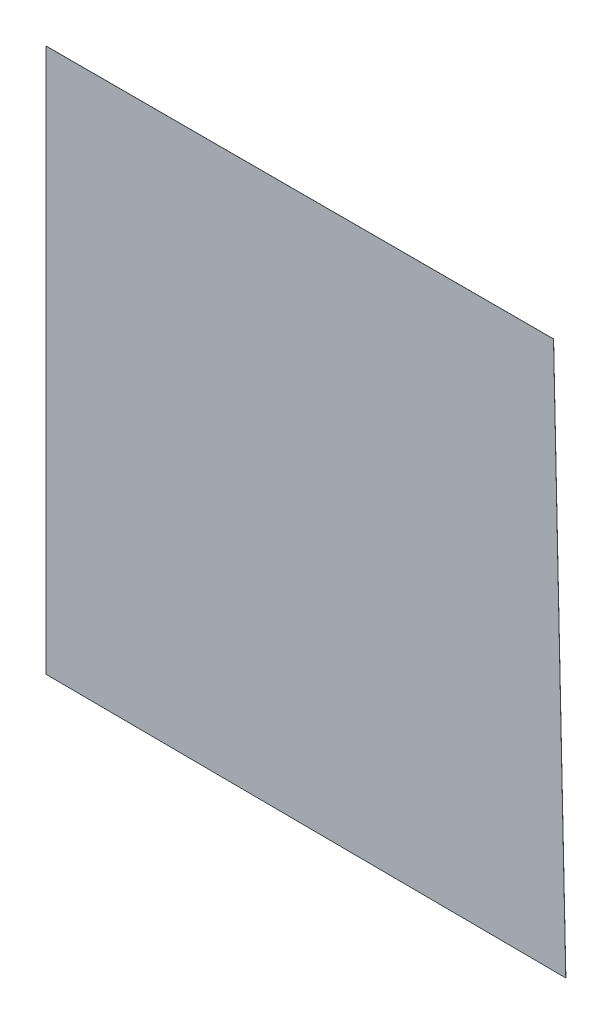
SolidWorks part; units mm, degrees
ref_plane "Alzado" through (0, 0, 0) normal (0, 0, 1) x (1, 0, 0)
ref_plane "Planta" through (0, 0, 0) normal (0, 1, 0) x (1, 0, 0)
ref_plane "Vista lateral" through (0, 0, 0) normal (1, 0, 0) x (0, 0, -1)
sketch "Croquis1" plane through (0, 0, 0) normal (0, 0, 1) x (1, 0, 0)
  line L0 (0, 0) -> (367.8609, -3505.2)
  line L1 (367.8609, -3505.2) -> (-11732.6991, -3406.3005)
  line L2 (-11732.6991, -3406.3005) -> (-11732.6991, 1226.6595)
  line L3 (-11732.6991, 1226.6595) -> (-6764.6695, 1180.9395)
  line L4 (-6764.6695, 1180.9395) -> (-6581.5791, -3448.4013)
  line L5 (-11732.6991, 1226.6595) -> (-11732.6991, 5798.6595)
  line L7 (-6764.6695, 1180.9395) -> (-6764.6695, 5844.3795)
  line L8 (-6764.6695, 1180.9395) -> (-4448.1895, 1180.9395)
  line L9 (-4448.1895, 1180.9395) -> (-4448.1895, -129.7005)
  line L10 (-853.0774, -24.8741) -> (0, 0)
  line L11 (-11732.6991, 5798.6595) -> (-11732.6991, 15552.2595)
  line L12 (-11732.6991, 15552.2595) -> (5945.7009, 15552.2595)
  line L13 (5945.7009, 15552.2595) -> (6206.8934, 1838.7467)
  line L14 (6206.8934, 1838.7467) -> (-251.7334, 1637.547)
  line L15 (-251.7334, 1637.547) -> (-1615.1032, 12371.711)
  line L16 (-1615.1032, 12371.711) -> (-9539.9032, 12371.711)
  line L17 (-9539.9032, 12371.711) -> (-9568.7108, 5818.5744)
  line L18 (-853.0774, -24.8741) -> (-251.7334, 1637.547)
  line L19 (6206.8934, 1838.7467) -> (6206.8934, -1209.2533)
  line L20 (367.8609, -3505.2) -> (4680.7809, -3505.2)
  line L21 (-6764.6695, 5844.3795) -> (-11732.6991, 5798.6595)
  line L22 (-4448.1895, -129.7005) -> (-853.0774, -24.8741)
  arc A0 (4680.7809, -3505.2) -> (6206.8934, -1209.2533) centre (4680.7809, -1850.0242) ccw
  point P6 (-6764.6695, 3512.6595)
  point P23 (-11732.6991, 3512.6595)
  point P24 (-613.9967, 1544.9466)
  point P25 (0, 0)
  point P26 (-1319.7617, 12363.7526)
  point P27 (0, 0)
  point P28 (0, 0)
  point P29 (0, 0)
  point P30 (0, 0)
  point P31 (0, 0)
  point P32 (0, 0)
  point P33 (0, 0)
  dimension "D7" = 4450.08
  dimension "D25" = 7620
  dimension "D1" = 17678.4
  dimension "D2" = 13716
  dimension "D3" = 9753.6
  dimension "D4" = 7924.8
  dimension "D5" = 6553.2
  dimension "D6" = 2164.08
  dimension "D8" = 3048
  dimension "D9" = 4312.92
  dimension "D10" = 6461.76
  dimension "D11" = 4968.24
  dimension "D12" = 4968.24
  dimension "D13" = 5151.12
  dimension "D14" = 2316.48
  dimension "D15" = 1310.64
  dimension "D16" = 10820.4
  dimension "D17" = 6949.44
  dimension "D18" = 4632.96
  dimension "D19" = 4572
  dimension "D20" = 4663.44
  dimension "D21" = 1767.84
  dimension "D22" = 853.44
  dimension "D23" = 3505.2
  dimension "D24" = 4632.96
sketch "Croquis2" plane through (0, 0, 0) normal (0, 0, 1) x (1, 0, 0)
  line L0 (-11732.6991, 15552.2595) -> (-11732.6991, -3406.3005)
  line L1 (-11732.6991, -3406.3005) -> (6373.7606, -3515.4011)
  line L2 (6373.7606, -3515.4011) -> (5945.7009, 15552.2595)
  line L3 (5945.7009, 15552.2595) -> (-11732.6991, 15552.2595)
  arc A0 (4680.7809, -3505.2) -> (6206.8934, -1209.2533) centre (4680.7809, -1850.0242) ccw construction
  point P3 (0, 0)
  point P5 (0, 0)
  point P7 (0, 0)
  point P10 (0, 0)
  point P11 (0, 0)
  point P12 (0, 0)
  point P13 (0, 0)
  point P14 (0, 0)
  point P16 (5945.7009, -3830.3929)
  point P17 (5945.7009, -3406.3005)
extrude "Saliente-Extruir1" add sketch "Croquis2" along normal blind 2.54
